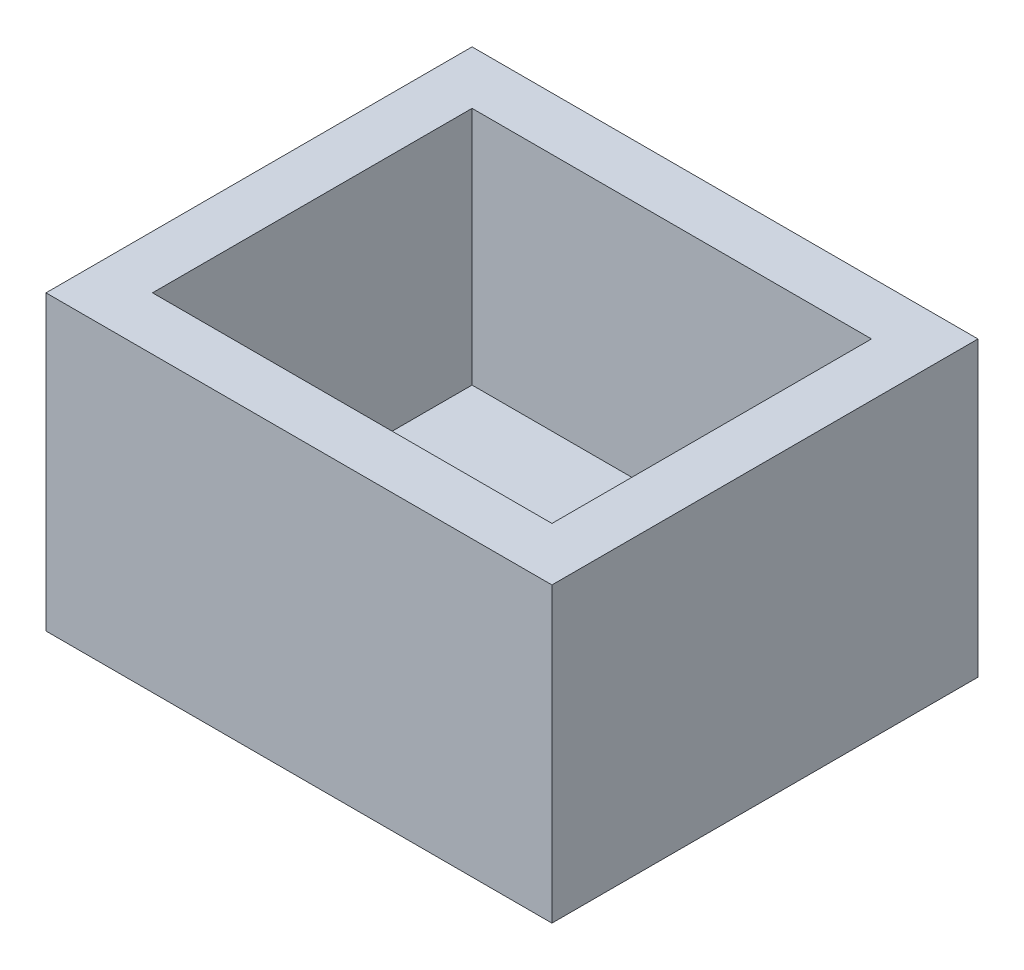
SolidWorks part; units mm, degrees
ref_plane "Front Plane" through (0, 0, 0) normal (0, 0, 1) x (1, 0, 0)
ref_plane "Top Plane" through (0, 0, 0) normal (0, 1, 0) x (1, 0, 0)
ref_plane "Right Plane" through (0, 0, 0) normal (1, 0, 0) x (0, 0, -1)
sketch "Sketch1" plane through (0, 0, 0) normal (0, 1, 0) x (1, 0, 0)
  line L1 (0, 0) -> (19, 0)
  line L2 (0, 0) -> (0, 16)
  line L3 (0, 16) -> (19, 16)
  line L4 (19, 0) -> (19, 16)
  dimension "D1" = 19
  dimension "D2" = 16
extrude "Boss-Extrude1" add sketch "Sketch1" along normal blind 11
shell "Shell1" thickness 2
sketch "Sketch2" plane through (0, 2, 0) normal (0, 1, 0) x (1, 0, 0)
  line L0 (16.0257, 11.528) -> (16.0257, 12.028) construction
  line L1 (16.0257, 3.908) -> (16.0257, 4.408) construction
  circle A0 centre (16.0257, 11.778) radius 0.625
  circle A1 centre (16.0257, 6.698) radius 0.625
  circle A2 centre (16.0257, 4.158) radius 0.625
  point P0 (16.0257, 11.778)
  point P1 (16.0257, 6.698)
  point P4 (16.0257, 4.158)
  point P6 (27.9882, 9.585)
  dimension "D1" = 1.25
  dimension "D2" = 1.25
  dimension "D3" = 1.25
extrude "Cut-Extrude1" cut sketch "Sketch2" against normal blind 10
